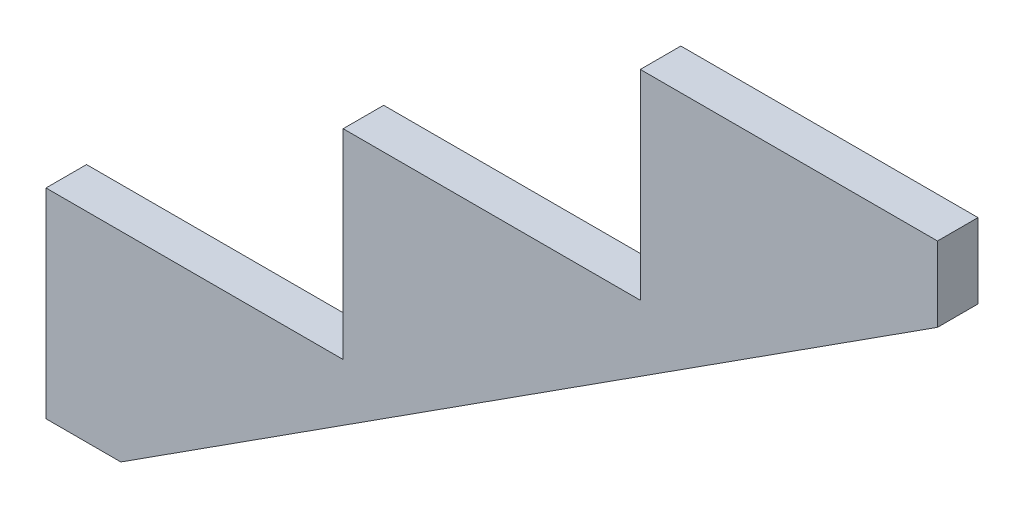
SolidWorks part; units mm, degrees
ref_plane "Front Plane" through (0, 0, 0) normal (0, 0, 1) x (1, 0, 0)
ref_plane "Top Plane" through (0, 0, 0) normal (0, 1, 0) x (1, 0, 0)
ref_plane "Right Plane" through (0, 0, 0) normal (1, 0, 0) x (0, 0, -1)
sketch "Sketch1" plane through (0, 0, 0) normal (0, 0, 1) x (1, 0, 0)
  line L8 (0, 187.96) -> (0, 0)
  line L10 (0, 187.96) -> (279.4, 187.96)
  line L11 (279.4, 187.96) -> (279.4, 375.92)
  line L12 (279.4, 375.92) -> (558.8, 375.92)
  line L13 (558.8, 375.92) -> (558.8, 563.88)
  line L14 (558.8, 563.88) -> (838.2, 563.88)
  line L15 (0, 0) -> (70.3483, 0)
  line L16 (70.3483, 0) -> (838.2, 493.5317)
  line L17 (838.2, 493.5317) -> (838.2, 563.88)
  line L18 (279.4, 375.92) -> (389.2682, 204.9837) construction
  dimension "D1" = 279.4
  dimension "D2" = 187.96
  dimension "D3" = 203.2
extrude "Boss-Extrude1" add sketch "Sketch1" along normal blind 38.1
